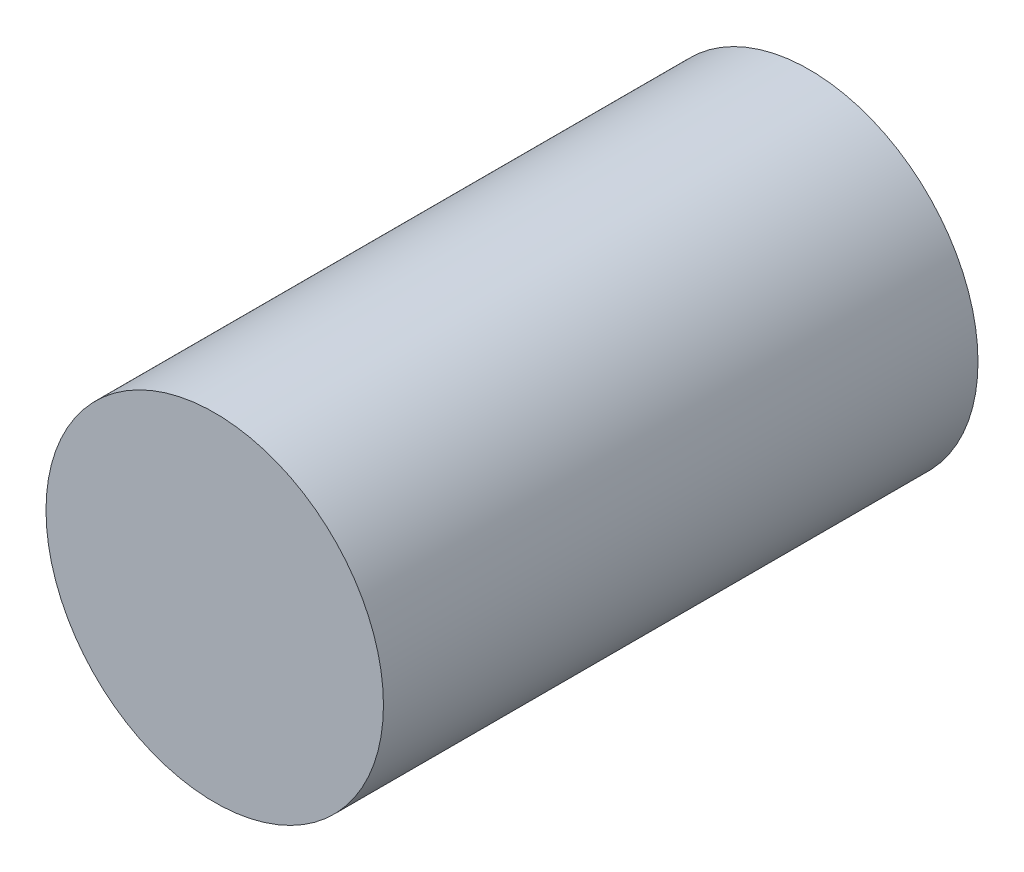
SolidWorks part; units mm, degrees
material "Acero aleado fundido"
ref_plane "Alzado" through (0, 0, 0) normal (0, 0, 1) x (1, 0, 0)
ref_plane "Planta" through (0, 0, 0) normal (0, 1, 0) x (1, 0, 0)
ref_plane "Vista lateral" through (0, 0, 0) normal (1, 0, 0) x (0, 0, -1)
sketch "Croquis1" plane through (0, 0, 0) normal (0, 0, 1) x (1, 0, 0)
  circle A0 centre (0, 0) radius 21
  dimension "D1" = 42
extrude "Saliente-Extruir1" add sketch "Croquis1" along normal blind 74
